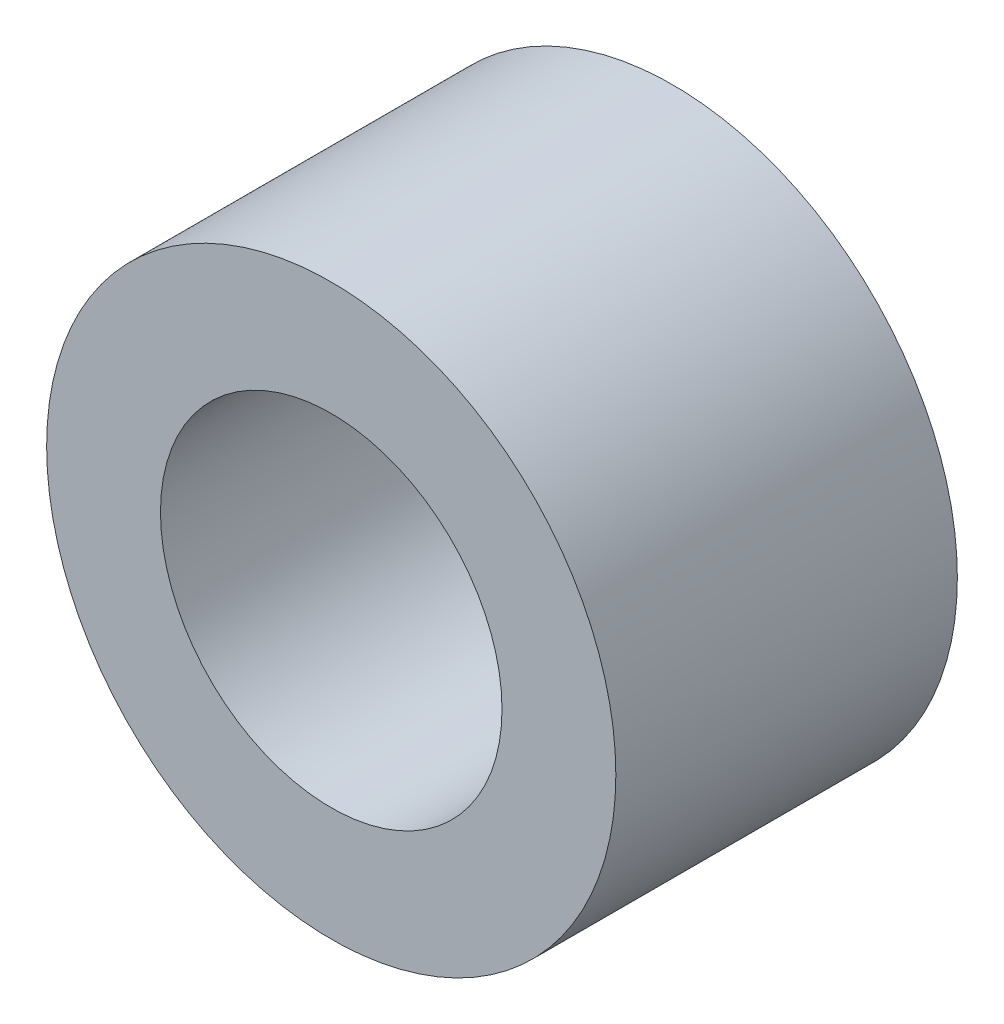
SolidWorks part; units mm, degrees
ref_plane "Front Plane" through (0, 0, 0) normal (0, 0, 1) x (1, 0, 0)
ref_plane "Top Plane" through (0, 0, 0) normal (0, 1, 0) x (1, 0, 0)
ref_plane "Right Plane" through (0, 0, 0) normal (1, 0, 0) x (0, 0, -1)
sketch "Sketch1" plane through (0, 0, 0) normal (0, 0, 1) x (1, 0, 0)
  circle A0 centre (0, 0) radius 25
  dimension "D1" = 50
extrude "Boss-Extrude1" add sketch "Sketch1" along normal mid plane 30
sketch "Sketch2" plane through (0, 0, 15) normal (0, 0, 1) x (1, 0, 0)
  circle A0 centre (0, 0) radius 15
extrude "Cut-Extrude1" cut sketch "Sketch2" against normal blind 112 and the other way blind 110
